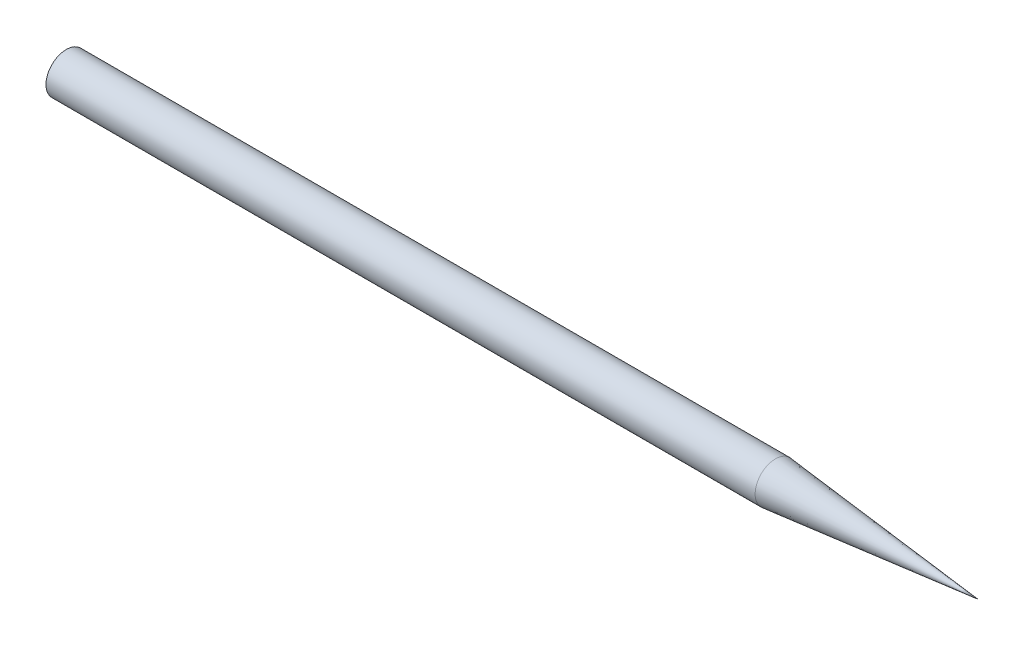
SolidWorks part; units mm, degrees
ref_plane "Front Plane" through (0, 0, 0) normal (0, 0, 1) x (1, 0, 0)
ref_plane "Top Plane" through (0, 0, 0) normal (0, 1, 0) x (1, 0, 0)
ref_plane "Right Plane" through (0, 0, 0) normal (1, 0, 0) x (0, 0, -1)
sketch "Sketch1" plane through (0, 0, 0) normal (0, 0, 1) x (1, 0, 0)
  line L0 (-67.5, 0) -> (67.5, 0)
  line L1 (67.5, 0) -> (37.5, 3)
  line L2 (37.5, 3) -> (-67.5, 3)
  line L3 (-67.5, 3) -> (-67.5, 0)
  point P6 (0, 0)
  dimension "D1" = 135
  dimension "D2" = 30
  dimension "D3" = 3
revolve "Revolve1" add sketch "Sketch1" angle 360 about L0
